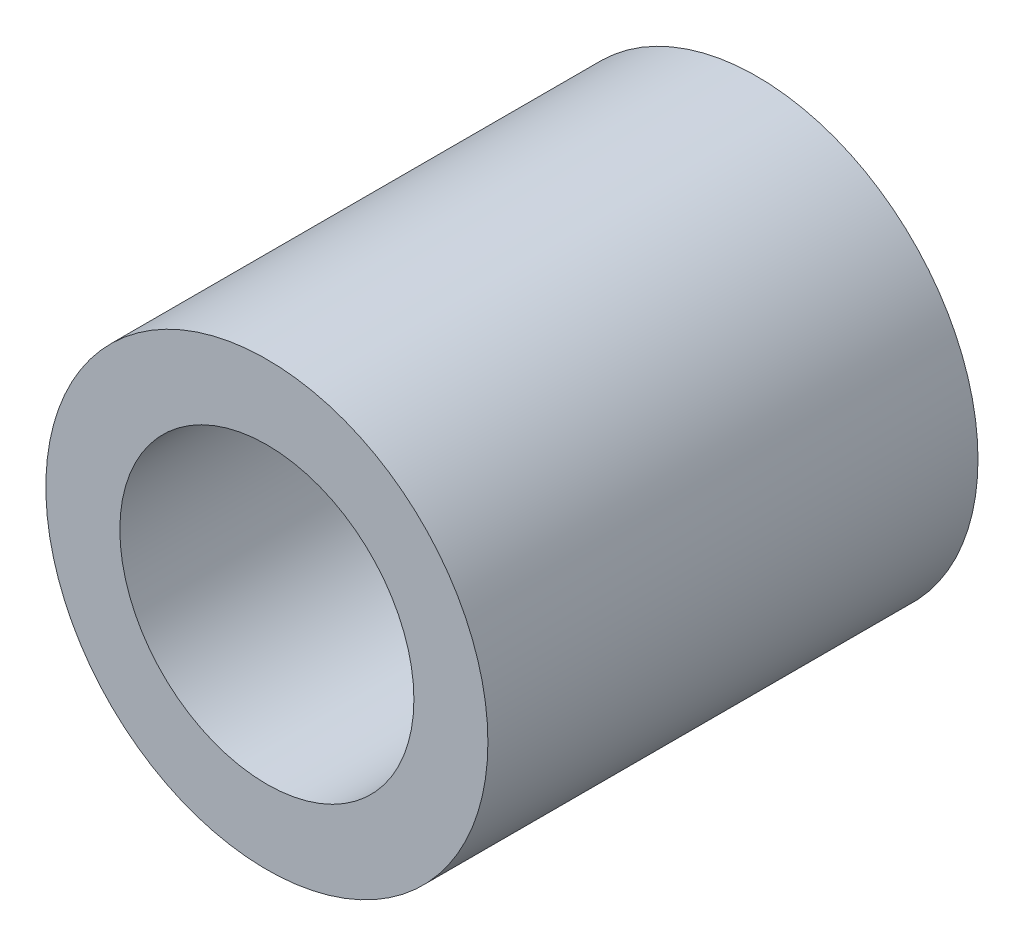
SolidWorks part; units mm, degrees
ref_plane "Front Plane" through (0, 0, 0) normal (0, 0, 1) x (1, 0, 0)
ref_plane "Top Plane" through (0, 0, 0) normal (0, 1, 0) x (1, 0, 0)
ref_plane "Right Plane" through (0, 0, 0) normal (1, 0, 0) x (0, 0, -1)
sketch "Sketch1" plane through (0, 0, 0) normal (0, 0, 1) x (1, 0, 0)
  circle A0 centre (0, 0) radius 4.51
  circle A1 centre (0, 0) radius 3
  dimension "D1" = 9.02
  dimension "ID" = 6
extrude "Extrude1" add sketch "Sketch1" along normal mid plane 10
sketch "Sketch2" plane through (0, 0, 0) normal (1, 0, 0) x (0, 0, -1)
  line L0 (-5, -3) -> (5, -3) construction
  line L3 (5, 3) -> (-5, 3) construction
  line L5 (-5, -3) -> (5, -3)
  line L6 (5, 3) -> (-5, 3)
sketch "Sketch4" plane through (0, 0, 5) normal (0, 0, 1) x (1, 0, 0)
  line L0 (0, 0) -> (-2.1213, 2.1213)
  line L1 (0, -5.5) -> (0, 5.5) construction
  circle A0 centre (0, 0) radius 3 construction
  dimension "D1" = 45
